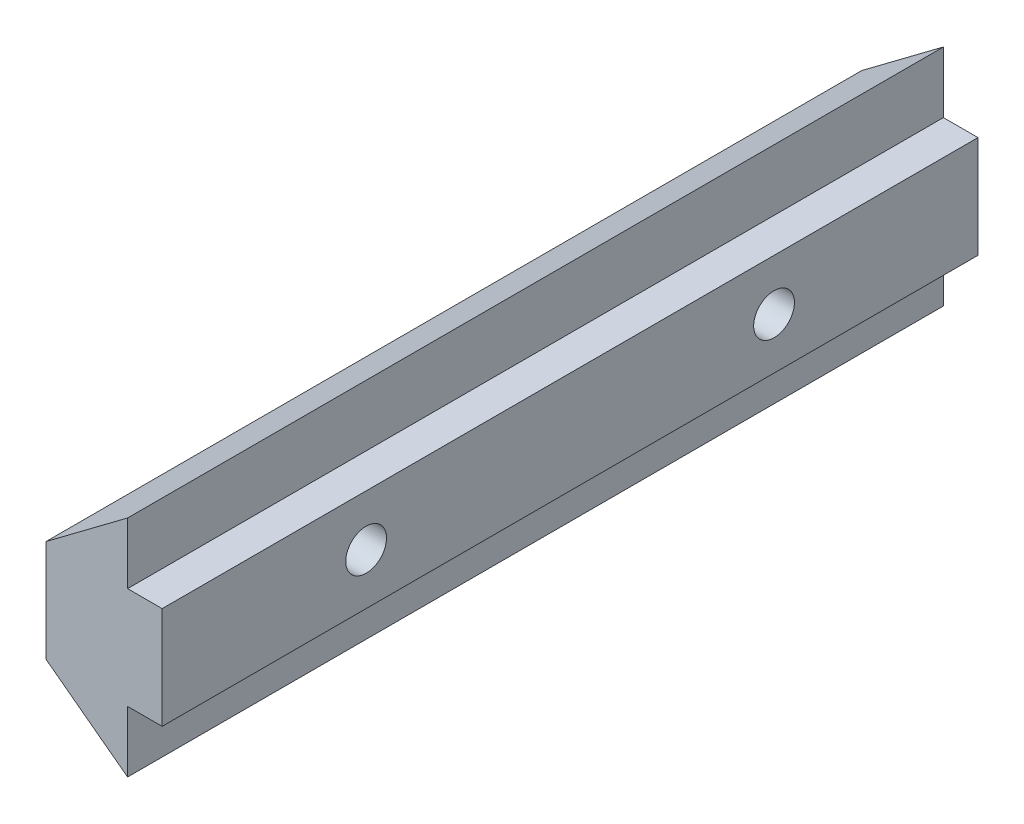
SolidWorks part; units mm, degrees
ref_plane "Plan de face" through (0, 0, 0) normal (0, 0, 1) x (1, 0, 0)
ref_plane "Plan de dessus" through (0, 0, 0) normal (0, 1, 0) x (1, 0, 0)
ref_plane "Plan de droite" through (0, 0, 0) normal (1, 0, 0) x (0, 0, -1)
sketch "ProfileRainureEsquisse" plane through (0, 0, 0) normal (0, 0, 1) x (1, 0, 0)
  line L0 (0, 0) -> (0, 5)
  line L1 (0, 5) -> (4, 8)
  line L2 (0, 0) -> (4, -3)
  line L3 (4, 8) -> (4, 5)
  line L4 (4, 5) -> (5.6958, 5)
  line L5 (5.6958, 5) -> (5.6958, 0)
  line L6 (5.6958, 0) -> (4, 0)
  line L7 (4, 0) -> (4, -3)
  dimension "D1" = 4
  dimension "D2" = 5.6958
  dimension "D3" = 5
  dimension "D4" = 8
extrude "Boss.-Extru.1" add sketch "ProfileRainureEsquisse" along normal blind 40
sketch "Esquisse1" plane through (5.6958, 0, 0) normal (1, 0, 0) x (0, 0, -1)
  line L0 (-40, 0) -> (-40, 5) construction
  circle A0 centre (-30, 2.5) radius 1
  point P2 (-40, 2.5)
  point P7 (-40, 2.5)
  point P10 (-40, 2.5)
  dimension "D1" = 2
  dimension "D2" = 10
extrude "Enlèv. mat.-Extru.1" cut sketch "Esquisse1" against normal through all
pattern_linear "Répétition linéaire2" count 2 spacing 20 along (0, 0, -1) of "Enlèv. mat.-Extru.1"
